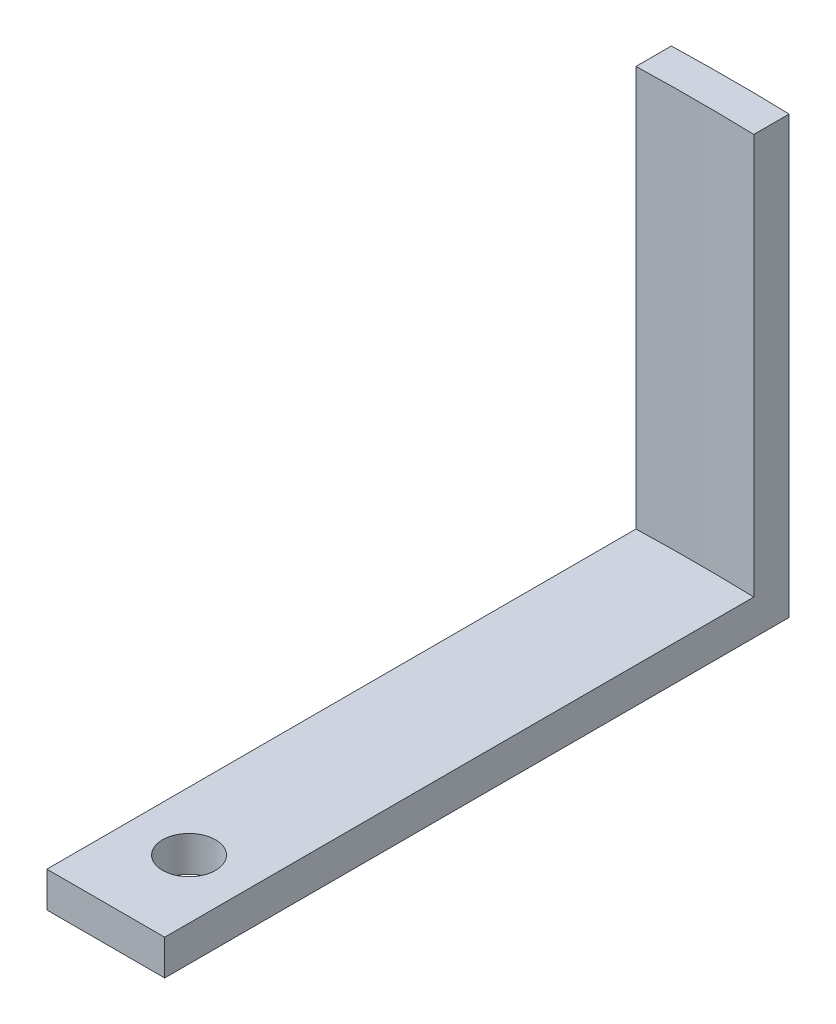
SolidWorks part; units mm, degrees
ref_plane "Front Plane" through (0, 0, 0) normal (0, 0, 1) x (1, 0, 0)
ref_plane "Top Plane" through (0, 0, 0) normal (0, 1, 0) x (1, 0, 0)
ref_plane "Right Plane" through (0, 0, 0) normal (1, 0, 0) x (0, 0, -1)
sketch "Sketch1" plane through (0, 0, 0) normal (0, 1, 0) x (1, 0, 0)
  line L0 (-5, 177.9298) -> (-5, 127.9298)
  line L1 (-5, 127.9298) -> (5, 127.9298)
  line L2 (5, 127.9298) -> (5, 177.9298)
  line L3 (0, 127.9298) -> (0, 178) construction
  line L4 (0, 178) -> (-30.7013, 178) construction
  arc A0 (-5, 177.9298) -> (5, 177.9298) centre (0, 0) cw
  dimension "D1" = 178
  dimension "D2" = 10
  dimension "D3" = 50
extrude "Boss-Extrude1" add sketch "Sketch1" along normal blind 3
sketch "Sketch2" plane through (0, 0, 0) normal (0, -1, 0) x (1, 0, 0)
  line L0 (5, -177.9298) -> (5, -180.9298)
  line L1 (-5, -180.9298) -> (-5, -177.9298)
  arc A0 (5, -177.9298) -> (-5, -177.9298) centre (0, 0) cw
  arc A1 (-5, -177.9298) -> (5, -177.9298) centre (0, 0) ccw construction
  arc A2 (5, -180.9298) -> (-5, -180.9298) centre (0, 0) cw
  dimension "D1" = 3
extrude "Boss-Extrude2" add sketch "Sketch2" against normal blind 37
sketch "Sketch3" plane through (0, 0, 0) normal (0, -1, 0) x (1, 0, 0)
  line L0 (0, -127.9298) -> (0, 0) construction
  line L1 (-5, -127.9298) -> (5, -127.9298) construction
  circle A0 centre (0, -135) radius 2.25
  dimension "D2" = 4.5
  dimension "D1" = 135
extrude "Cut-Extrude1" cut sketch "Sketch3" against normal up to next
